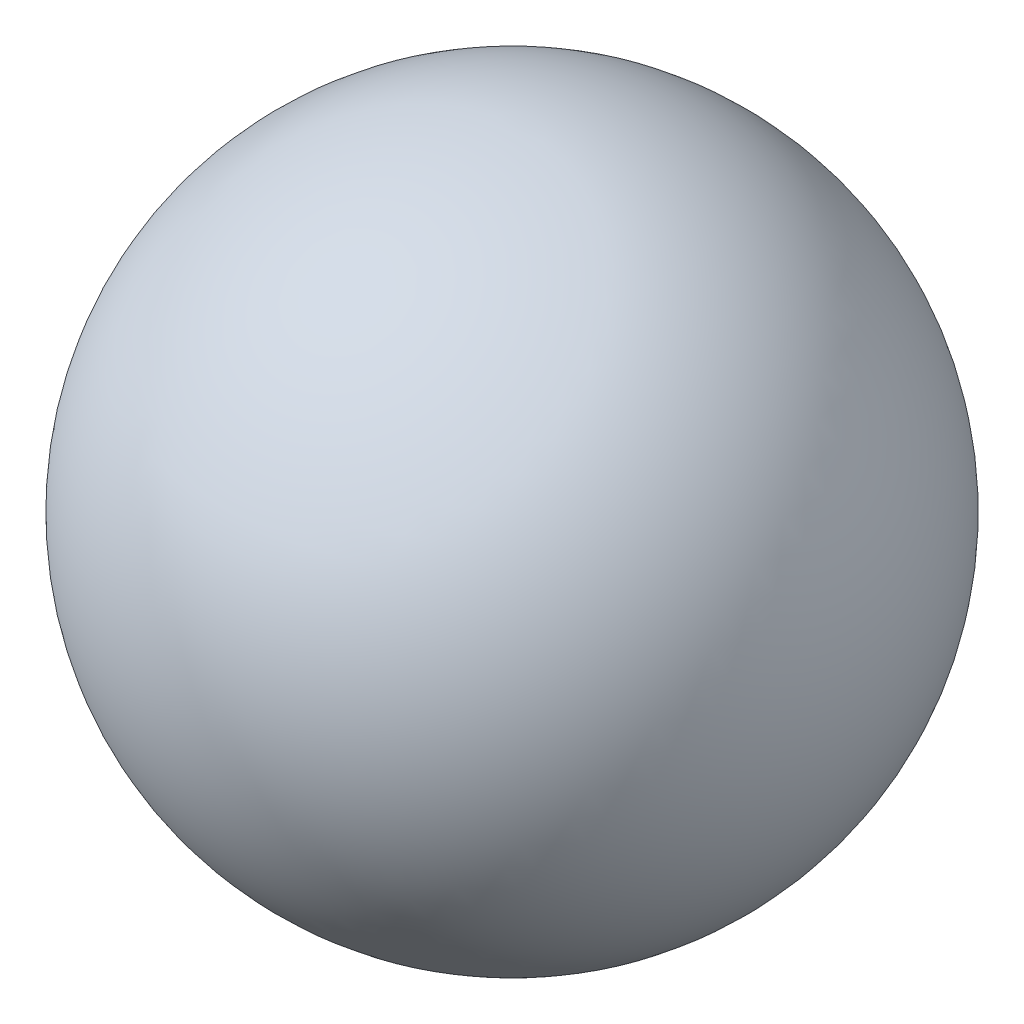
SolidWorks part; units mm, degrees
ref_plane "Front Plane" through (0, 0, 0) normal (0, 0, 1) x (1, 0, 0)
ref_plane "Top Plane" through (0, 0, 0) normal (0, 1, 0) x (1, 0, 0)
ref_plane "Right Plane" through (0, 0, 0) normal (1, 0, 0) x (0, 0, -1)
sketch "Sketch1" plane through (0, 0, 0) normal (0, 0, 1) x (1, 0, 0)
  line L0 (0, 32.5) -> (0, -32.5) construction
  line L1 (0, 32.5) -> (0, -32.5)
  arc A0 (0, 32.5) -> (0, -32.5) centre (0, 0) ccw
revolve "Revolve1" add sketch "Sketch1" angle 360 about L0
